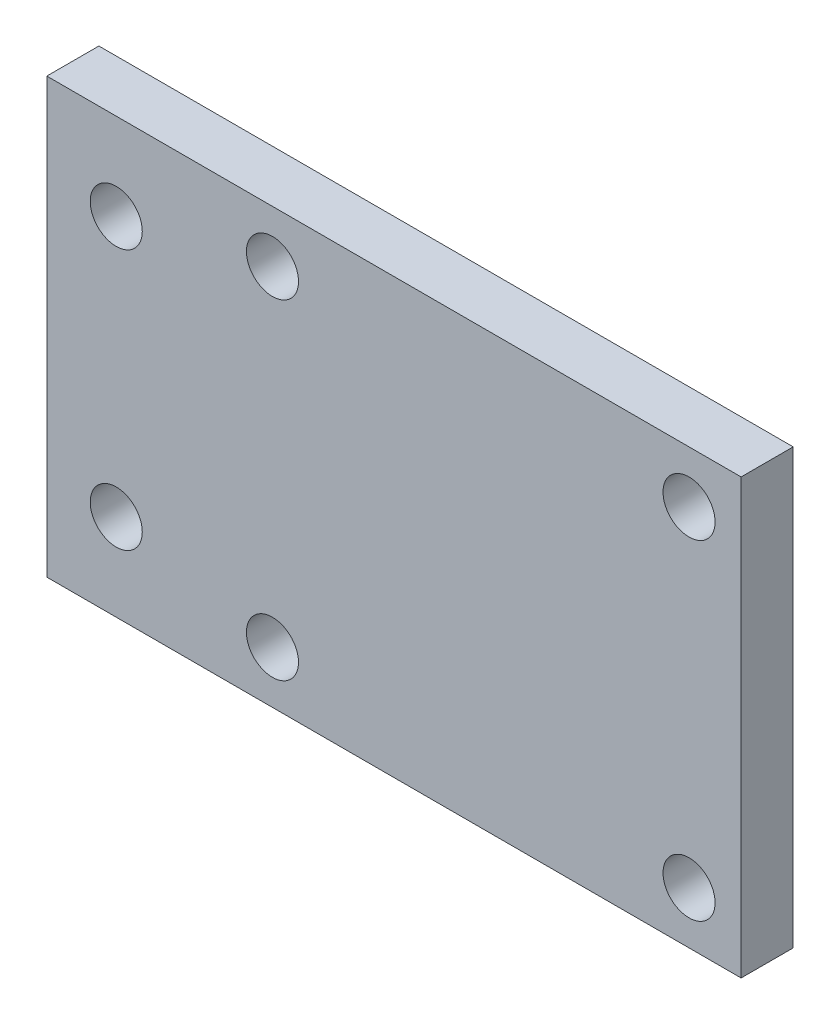
SolidWorks part; units mm, degrees
ref_plane "前视基准面" through (0, 0, 0) normal (0, 0, 1) x (1, 0, 0)
ref_plane "上视基准面" through (0, 0, 0) normal (0, 1, 0) x (1, 0, 0)
ref_plane "右视基准面" through (0, 0, 0) normal (1, 0, 0) x (0, 0, -1)
sketch "草图1" plane through (0, 0, 0) normal (0, 0, 1) x (1, 0, 0)
  line L1 (-20, -12.5) -> (20, -12.5)
  line L2 (-20, -12.5) -> (-20, 12.5)
  line L3 (-20, 12.5) -> (20, 12.5)
  line L4 (20, -12.5) -> (20, 12.5)
  line L5 (-20, -12.5) -> (20, 12.5) construction
  line L6 (-20, 12.5) -> (20, -12.5) construction
  line L7 (-7, -9.5) -> (17, -9.5) construction
  line L8 (-7, -9.5) -> (-7, 9.5) construction
  line L9 (-7, 9.5) -> (17, 9.5) construction
  line L10 (17, -9.5) -> (17, 9.5) construction
  line L11 (-7, -9.5) -> (17, 9.5) construction
  line L12 (-7, 9.5) -> (17, -9.5) construction
  circle A0 centre (-7, 9.5) radius 1.5
  circle A1 centre (17, 9.5) radius 1.5
  circle A2 centre (-7, -9.5) radius 1.5
  circle A3 centre (17, -9.5) radius 1.5
  circle A4 centre (-16, 7.5) radius 1.5
  circle A5 centre (-16, -7.5) radius 1.5
  point P0 (0, 0)
  point P6 (5, 0)
  point P19 (0, 0)
  point P20 (6.2584, -0.7089)
  dimension "D3" = 15
  dimension "D4" = 5
  dimension "D5" = 3
  dimension "D6" = 4
  dimension "D10" = 4
  dimension "D1" = 40
  dimension "D2" = 25
  dimension "D7" = 5
  dimension "D8" = 19
  dimension "D9" = 24
extrude "凸台-拉伸1" add sketch "草图1" along normal blind 3
